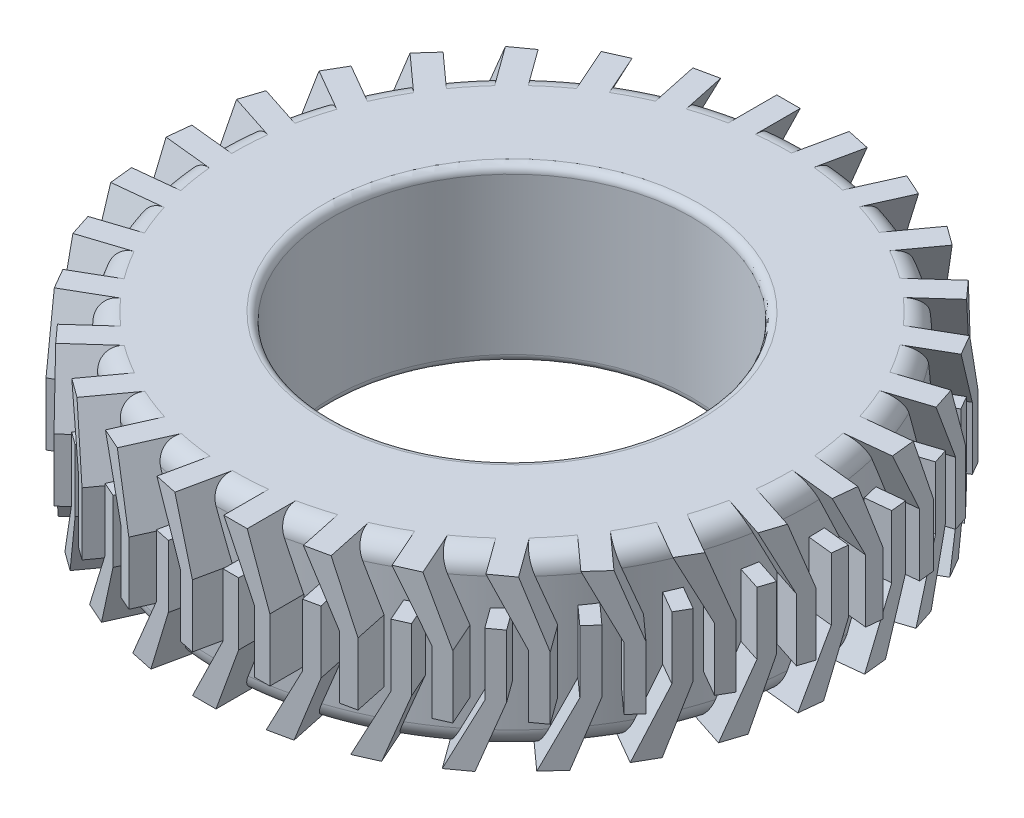
SolidWorks part; units mm, degrees
material "Natural Rubber"
ref_plane "Front" through (0, 0, 0) normal (0, 0, 1) x (1, 0, 0)
ref_plane "Top" through (0, 0, 0) normal (0, 1, 0) x (1, 0, 0)
ref_plane "Right" through (0, 0, 0) normal (1, 0, 0) x (0, 0, -1)
sketch "Sketch1" plane through (0, 0, 0) normal (0, 0, 1) x (1, 0, 0)
  line L0 (0, 0) -> (0, 141.534) construction
  line L1 (355, 220) -> (240, 220)
  line L2 (380, 195) -> (380, 25)
  line L3 (355, 0) -> (240, 0)
  line L4 (230, 210) -> (230, 10)
  line L5 (380, 220) -> (230, 0) construction
  line L6 (380, 0) -> (230, 220) construction
  arc A0 (240, 0) -> (230, 10) centre (240, 10) cw
  arc A1 (240, 220) -> (230, 210) centre (240, 210) ccw
  arc A2 (380, 25) -> (355, 0) centre (355, 25) cw
  arc A3 (355, 220) -> (380, 195) centre (355, 195) cw
  point P0 (305, 110)
  point P20 (0, 0)
  dimension "D1" = 10
  dimension "D2" = 25
  dimension "D3" = 220
  dimension "D4" = 150
  dimension "D5" = 230
revolve "Revolve1" add sketch "Sketch1" angle 360 about L0
ref_plane "Plane1" through (0, 0, 380) normal (0, 0, 1) x (1, 0, 0)
sketch "Sketch2" plane through (0, 0, 380) normal (0, 0, 1) x (1, 0, 0)
  line L5 (80, 140) -> (40.9814, 220)
  line L11 (-240, 0) -> (240, 0) construction
  line L12 (0, 0) -> (0, 10.9368) construction
  line L13 (40, 160) -> (60, 160)
  line L14 (40, 160) -> (40, 80)
  line L16 (60, 160) -> (60, 80)
  line L17 (40, 160) -> (60, 80) construction
  line L18 (40, 80) -> (60, 160) construction
  line L19 (0.9814, 0) -> (30.9814, 0)
  line L20 (40, 80) -> (0.9814, 0)
  line L21 (60, 80) -> (30.9814, 0)
  line L24 (80, 140) -> (80, 60)
  line L25 (80, 60) -> (100, 60)
  line L26 (100, 140) -> (100, 60)
  line L27 (80, 140) -> (100, 60) construction
  line L28 (80, 60) -> (100, 140) construction
  line L29 (100, 140) -> (70.9814, 220)
  line L30 (240, 220) -> (-240, 220) construction
  line L31 (70.9814, 220) -> (40.9814, 220)
  point P0 (90, 100)
  point P8 (50, 120)
  dimension "D2" = 206
  dimension "D3" = 80
  dimension "D4" = 80
  dimension "D5" = 20
  dimension "D6" = 30
  dimension "D7" = 20
  dimension "D8" = 30
  dimension "D9" = 20
  dimension "D10" = 206
  dimension "D11" = 20
  dimension "D12" = 80
  dimension "D13" = 80
  dimension "D14" = 20
  dimension "D15" = 50
extrude "Boss-Extrude2" add sketch "Sketch2" along normal blind 30 and the other way up to body
pattern_circular "CirPattern1" count 30 over 360 about axis through (0, 0, 0) along (0, 1, 0) of "Boss-Extrude2"
